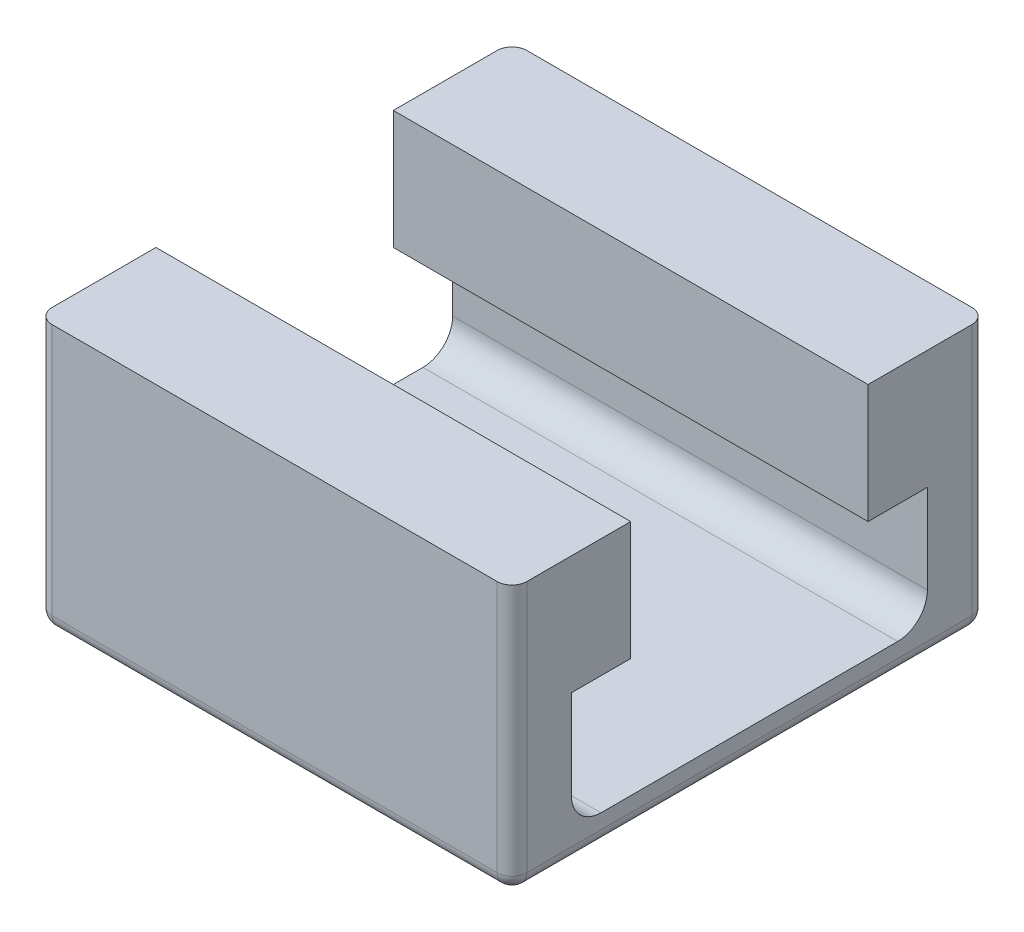
SolidWorks part; units mm, degrees
ref_plane "前基準面" through (0, 0, 0) normal (0, 0, 1) x (1, 0, 0)
ref_plane "上基準面" through (0, 0, 0) normal (0, 1, 0) x (1, 0, 0)
ref_plane "右基準面" through (0, 0, 0) normal (1, 0, 0) x (0, 0, -1)
sketch "草圖1" plane through (0, 0, 0) normal (1, 0, 0) x (0, 0, -1)
  line L0 (0, 0) -> (0, 4.5)
  line L1 (0, 0) -> (8, 0)
  line L2 (0, 4.5) -> (2, 4.5)
  line L3 (2, 4.5) -> (2, 2.5)
  line L4 (2, 2.5) -> (1, 2.5)
  line L5 (1, 2.5) -> (1, 1)
  line L6 (8, 0) -> (8, 4.5)
  line L7 (8, 4.5) -> (6, 4.5)
  line L8 (6, 4.5) -> (6, 2.5)
  line L9 (6, 2.5) -> (7, 2.5)
  line L10 (7, 2.5) -> (7, 1)
  line L11 (6.5, 0.5) -> (1.5, 0.5)
  arc A0 (6.5, 0.5) -> (7, 1) centre (6.5, 1) ccw
  arc A1 (1, 1) -> (1.5, 0.5) centre (1.5, 1) ccw
  dimension "D1" = 0.5
extrude "填料-伸長1" add sketch "草圖1" against normal blind 8
fillet "圓角1" radius 0.25 8 edges at (-4, 0, -8) (-8, 2.25, -8) (-4, 0, 0) (-8, 0, -4) (-8, 2.25, 0) (0, 0, -4) (0, 2.25, -8) (0, 2.25, 0)
